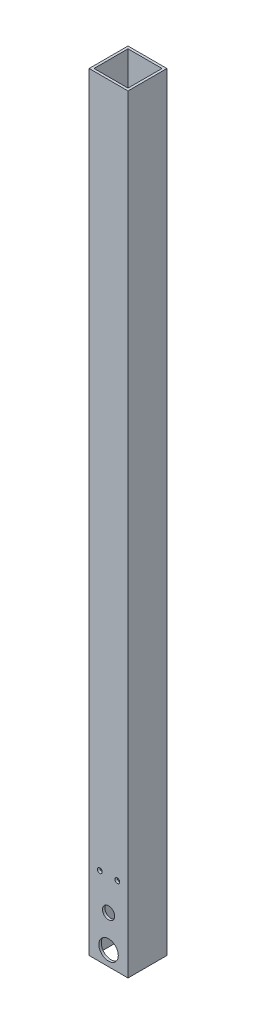
SolidWorks part; units mm, degrees
material "1060 Alloy"
ref_plane "Front Plane" through (0, 0, 0) normal (0, 0, 1) x (1, 0, 0)
ref_plane "Top Plane" through (0, 0, 0) normal (0, 1, 0) x (1, 0, 0)
ref_plane "Right Plane" through (0, 0, 0) normal (1, 0, 0) x (0, 0, -1)
sketch "Sketch1" plane through (0, 0, 0) normal (0, 1, 0) x (1, 0, 0)
  line L0 (-11.1125, 11.1125) -> (-11.1125, -11.1125)
  line L1 (-12.7, 12.7) -> (12.7, 12.7)
  line L2 (-12.7, 12.7) -> (-12.7, -12.7)
  line L3 (-12.7, -12.7) -> (12.7, -12.7)
  line L4 (12.7, 12.7) -> (12.7, -12.7)
  line L5 (-12.7, 12.7) -> (12.7, -12.7) construction
  line L6 (-12.7, -12.7) -> (12.7, 12.7) construction
  line L7 (-11.1125, -11.1125) -> (11.1125, -11.1125)
  line L8 (11.1125, 11.1125) -> (11.1125, -11.1125)
  line L9 (-11.1125, 11.1125) -> (11.1125, 11.1125)
  point P0 (0, 0)
  dimension "D1" = 25.4
  dimension "D2" = 25.4
  dimension "D3" = 1.5875
extrude "Boss-Extrude1" add sketch "Sketch1" along normal blind 501.65
sketch "Sketch4" plane through (0, 0, 12.7) normal (0, 0, 1) x (1, 0, 0)
  line L0 (0, 0) -> (0, 9.525) construction
  line L1 (-12.7, 0) -> (12.7, 0) construction
  circle A0 centre (0, 9.525) radius 6.35
  dimension "D1" = 12.7
  dimension "D2" = 9.525
extrude "Cut-Extrude1" cut sketch "Sketch4" against normal through all
sketch "Sketch5" plane through (0, 0, -12.7) normal (0, 0, -1) x (-1, 0, 0)
  line L0 (-12.7, 0) -> (12.7, 0) construction
  line L1 (-12.7, 51.5178) -> (12.7, 51.5178) construction
  line L2 (-12.7, 501.65) -> (-12.7, 0) construction
  line L3 (12.7, 501.65) -> (12.7, 0) construction
  line L4 (5.7096, 51.5178) -> (-5.7096, 51.5178) construction
  circle A2 centre (-5.7096, 51.5178) radius 1.5875
  circle A3 centre (5.7096, 51.5178) radius 1.5875
  point P15 (0, 51.5178)
  dimension "D2" = 3.175
  dimension "D1" = 11.4193
  dimension "D3" = 51.5178
extrude "Cut-Extrude2" cut sketch "Sketch5" against normal through all
sketch "Sketch7" plane through (0, 0, 12.7) normal (0, 0, 1) x (1, 0, 0)
  line L0 (-12.7, 501.65) -> (-12.7, 0) construction
  line L1 (-12.7, 0) -> (12.7, 0) construction
  circle A1 centre (0, 30.5023) radius 3.9688
  dimension "D3" = 7.9375
  dimension "D1" = 12.7
  dimension "D2" = 30.5023
extrude "Cut-Extrude3" cut sketch "Sketch7" against normal up to surface (1.5875 mm away) up to face at (4.1221, 51.5178, 11.1125)
